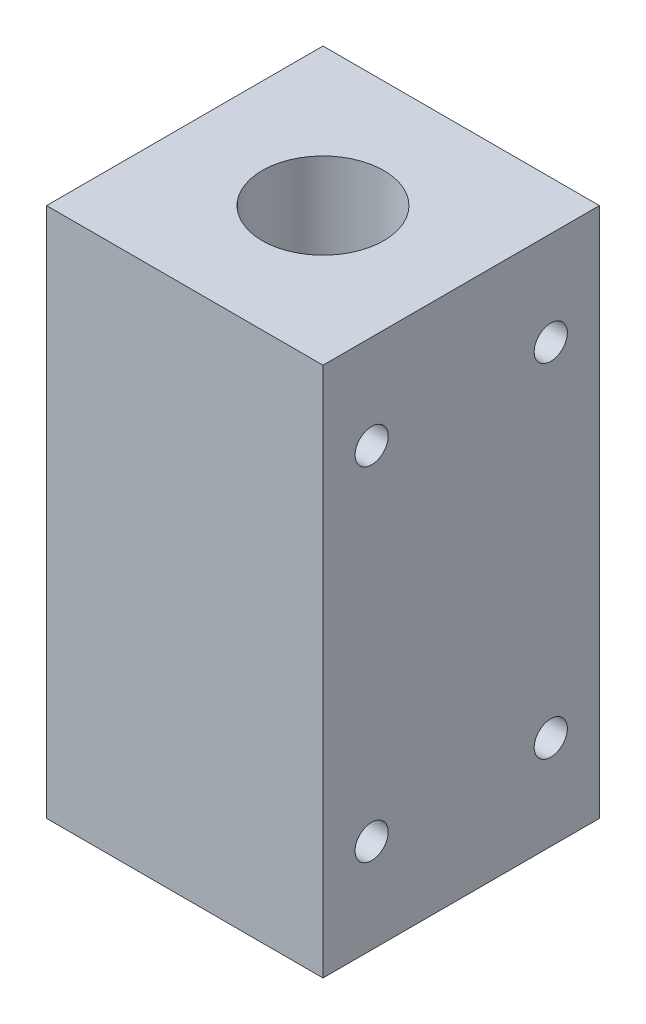
SolidWorks part; units mm, degrees
ref_plane "前视基准面" through (0, 0, 0) normal (0, 0, 1) x (1, 0, 0)
ref_plane "上视基准面" through (0, 0, 0) normal (0, 1, 0) x (1, 0, 0)
ref_plane "右视基准面" through (0, 0, 0) normal (1, 0, 0) x (0, 0, -1)
sketch "草图1" plane through (0, 0, 0) normal (0, 1, 0) x (1, 0, 0)
  line L1 (12.5, 12.5) -> (-12.5, 12.5)
  line L2 (12.5, 12.5) -> (12.5, -12.5)
  line L3 (12.5, -12.5) -> (-12.5, -12.5)
  line L4 (-12.5, 12.5) -> (-12.5, -12.5)
  line L5 (12.5, 12.5) -> (-12.5, -12.5) construction
  line L6 (12.5, -12.5) -> (-12.5, 12.5) construction
  circle A0 centre (0, 0) radius 5.5
  point P0 (0, 0)
  dimension "D3" = 11
  dimension "D1" = 25
  dimension "D2" = 25
extrude "凸台-拉伸1" add sketch "草图1" along normal blind 48
sketch "草图2" plane through (12.5, 0, 0) normal (1, 0, 0) x (0, 0, -1)
  line L0 (-12.5, 0) -> (12.5, 0) construction
  line L1 (12.5, 48) -> (12.5, 0) construction
  line L2 (0, 48) -> (0, 0) construction
  line L3 (-12.5, 48) -> (12.5, 48) construction
  line L4 (-12.5, 24) -> (12.5, 24) construction
  line L5 (-12.5, 48) -> (-12.5, 0) construction
  circle A0 centre (8.1, 8.5) radius 1.5
  circle A1 centre (-8.1, 8.5) radius 1.5
  circle A2 centre (-8.1, 39.5) radius 1.5
  circle A3 centre (8.1, 39.5) radius 1.5
  dimension "D3" = 3
  dimension "D1" = 8.5
  dimension "D2" = 4.4
extrude "切除-拉伸1" cut sketch "草图2" against normal blind 5
